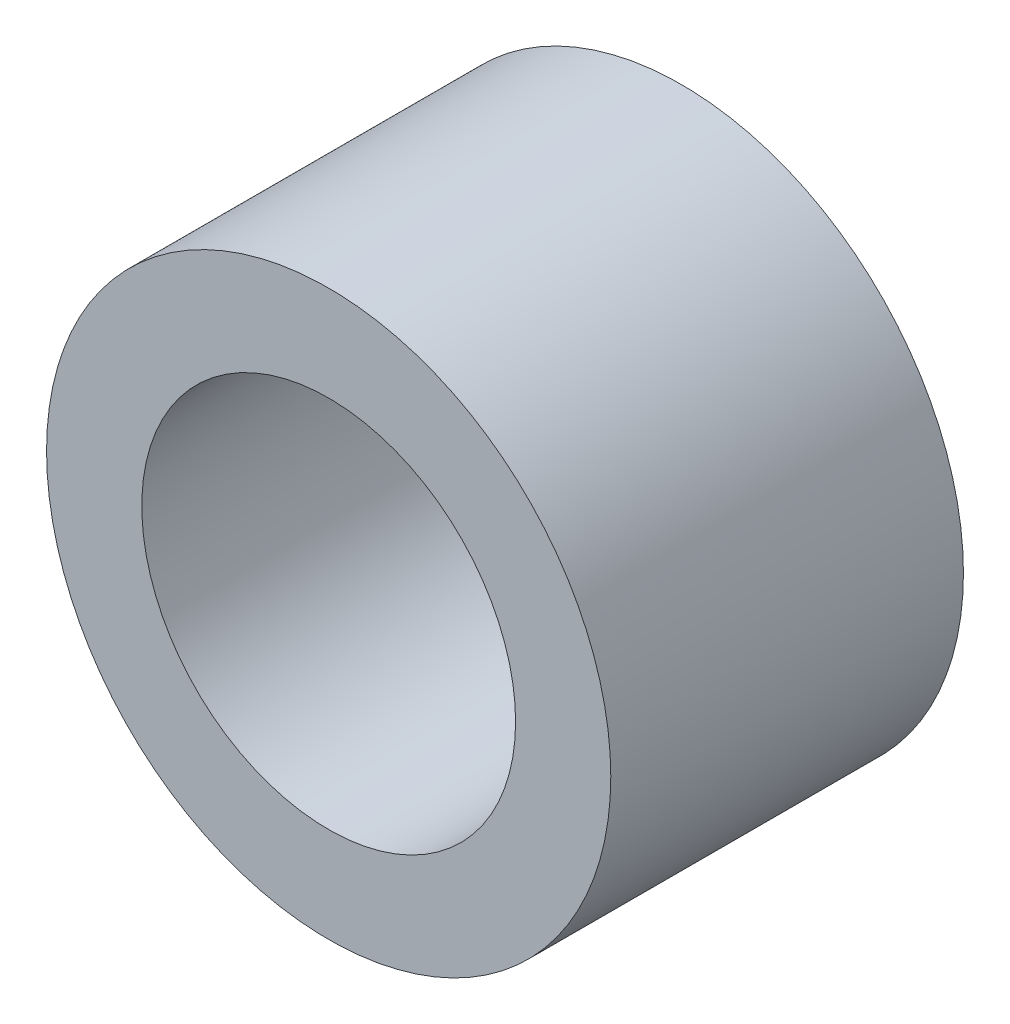
SolidWorks part; units mm, degrees
ref_plane "Front Plane" through (0, 0, 0) normal (0, 0, 1) x (1, 0, 0)
ref_plane "Top Plane" through (0, 0, 0) normal (0, 1, 0) x (1, 0, 0)
ref_plane "Right Plane" through (0, 0, 0) normal (1, 0, 0) x (0, 0, -1)
sketch "Sketch1" plane through (0, 0, 0) normal (0, 0, 1) x (1, 0, 0)
  line L0 (0, 2.65) -> (0, 4) construction
  line L1 (0, -2.65) -> (0, -4) construction
  circle A0 centre (0, 0) radius 4
  circle A1 centre (0, 0) radius 2.65
  dimension "OD" = 8
  dimension "ID" = 5.3
sketch "Sketch2" plane through (0, 0, 0) normal (1, 0, 0) x (0, 0, -1)
  line L0 (-2.5, 2.65) -> (2.5, 2.65) construction
  line L1 (-2.5, -2.65) -> (2.5, -2.65) construction
  line L2 (-2.5, -4) -> (2.5, -4) construction
  line L3 (-2.5, 4) -> (2.5, 4) construction
  dimension "Length" = 5
extrude "Extrude1" add sketch "Sketch1" along normal up to vertex (2.5 mm away) and the other way up to vertex (2.5 mm away) up to point (0, 2.65, 2.5) other way up to point (0, 2.65, -2.5)
sketch "Sketch3" plane through (0, 0, 2.5) normal (0, 0, 1) x (1, 0, 0)
  circle A0 centre (0, 0) radius 2.65 construction
  circle A3 centre (0, 0) radius 2.65
  point P3 (-2.65, 0)
